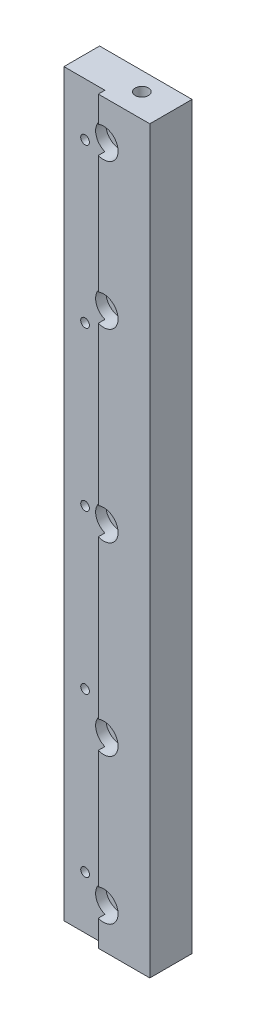
SolidWorks part; units mm, degrees
material "1023 Листовая углеродистая сталь (SS)"
ref_plane "Front" through (0, 0, 0) normal (0, 0, 1) x (1, 0, 0)
ref_plane "Top" through (0, 0, 0) normal (0, 1, 0) x (1, 0, 0)
ref_plane "Right" through (0, 0, 0) normal (1, 0, 0) x (0, 0, -1)
sketch "Sketch1" plane through (0, 0, 0) normal (0, 0, 1) x (1, 0, 0)
  line L1 (-17.5, 140) -> (17.5, 140)
  line L2 (-17.5, 140) -> (-17.5, -140)
  line L3 (-17.5, -140) -> (17.5, -140)
  line L4 (17.5, 140) -> (17.5, -140)
  line L5 (-17.5, 140) -> (17.5, -140) construction
  line L6 (-17.5, -140) -> (17.5, 140) construction
  point P0 (0, 0)
  dimension "D1" = 280
  dimension "D2" = 35
extrude "Extrude1" add sketch "Sketch1" along normal blind 16
sketch "Sketch2" plane through (0, -140, 0) normal (0, -1, 0) x (1, 0, 0)
  line L1 (-17.5, 16) -> (-2, 16)
  line L2 (-17.5, 16) -> (-17.5, 13.5)
  line L3 (-17.5, 13.5) -> (-2, 13.5)
  line L4 (-2, 16) -> (-2, 13.5)
  dimension "D1" = 2.5
  dimension "D2" = 15.5
extrude "Extrude2" cut sketch "Sketch2" against normal up to next
hole_wizard "M4 Tapped Hole1" positions "Sketch3" profile "Sketch4" tap size "M4" standard "DIN" end condition through all
sketch "Sketch3" plane through (0, 0, 13.5) normal (0, 0, 1) x (1, 0, 0)
  line L0 (-2, 140) -> (-2, -140) construction
  line L1 (-17.5, -140) -> (-2, -140) construction
  point P0 (-9.5, -120)
  point P12 (-9.5, -60)
  point P13 (-9.5, 0)
  point P14 (-9.5, 60)
  point P15 (-9.5, 120)
  dimension "D1" = 7.5
  dimension "D2" = 20
  dimension "D3" = 5
sketch "Sketch4" plane through (-9.5, -120, 13.5) normal (1, 0, 0) x (0, -1, 0)
  line L0 (0, 0) -> (0, 13.5)
  line L1 (0, 13.5) -> (1.65, 13.5)
  line L2 (1.65, 13.5) -> (1.65, 0)
  line L5 (1.65, 0) -> (0, 0)
  line L11 (0, -6.35) -> (0, 107.95) construction
  dimension "Диаметр проходного сверла" = 3.3
  dimension "Глубина проходного сверла" = 13.5
cosmetic thread "Cosmetic Thread1" parameters "D2"=4
cosmetic thread "Cosmetic Thread2" parameters "D2"=4
cosmetic thread "Cosmetic Thread3" parameters "D2"=4
cosmetic thread "Cosmetic Thread4" parameters "D2"=4
cosmetic thread "Cosmetic Thread5" parameters "D2"=4
hole_wizard "M6 Tapped Hole1" positions "Sketch5" profile "Sketch6" tap size "M6" standard "DIN" end condition through all
sketch "Sketch5" plane through (0, -140, 0) normal (0, -1, 0) x (-1, 0, 0)
  point P0 (-5.5, -7)
sketch "Sketch6" plane through (5.5, -140, 7) normal (1, 0, 0) x (0, 0, -1)
  line L0 (0, 0) -> (0, 280)
  line L1 (0, 280) -> (2.5, 280)
  line L2 (2.5, 280) -> (2.5, 0)
  line L5 (2.5, 0) -> (0, 0)
  line L11 (0, -6.35) -> (0, 107.95) construction
  dimension "Диаметр проходного сверла" = 5
  dimension "Глубина проходного сверла" = 280
cosmetic thread "Cosmetic Thread6" parameters "D2"=6
hole_wizard "CBORE for M6 Hex Socket Head Cap Screw1" positions "Sketch7" profile "Sketch8" counterbore size "M6" standard "DIN"
sketch "Sketch7" plane through (0, 0, 16) normal (0, 0, 1) x (1, 0, 0)
  point P0 (0, 125)
  point P3 (0, 70)
  point P6 (0, 0)
  point P9 (0, -70)
  point P12 (0, -125)
sketch "Sketch8" plane through (0, 125, 16) normal (1, 0, 0) x (0, -1, 0)
  line L0 (0, 0) -> (0, 30.9828)
  line L1 (0, 30.9828) -> (3.3, 29)
  line L2 (3.3, 29) -> (3.3, 6.4)
  line L3 (3.3, 6.4) -> (5.5, 6.4)
  line L4 (5.5, 6.4) -> (5.5, 0)
  line L5 (5.5, 0) -> (0, 0)
  line L10 (0, 30.9828) -> (-3.3, 29) construction
  line L11 (0, -6.35) -> (0, 107.95) construction
  dimension "Диаметр отверстия" = 6.6
  dimension "Глубина отверстия" = 29
  dimension "Диаметр цековки" = 11
  dimension "Глубина цековки" = 6.4
  dimension "Угол заточки сверла" = 118
